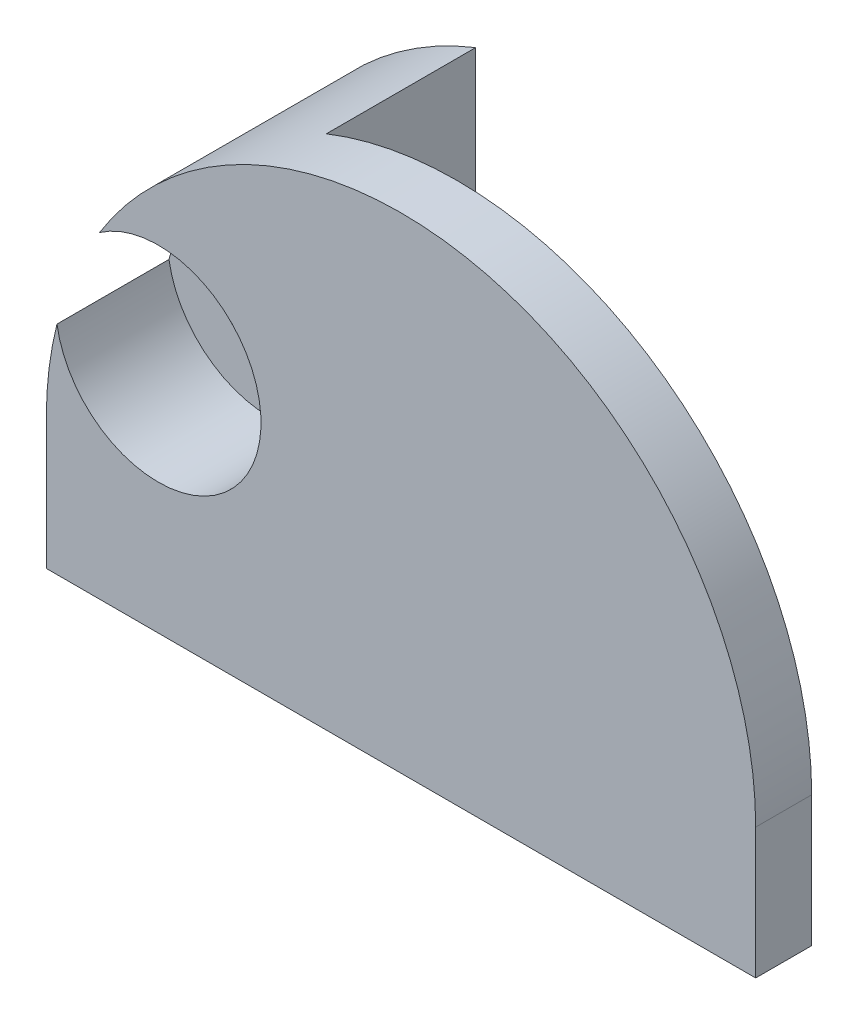
SolidWorks part; units mm, degrees
ref_plane "Plano frontal" through (0, 0, 0) normal (0, 0, 1) x (1, 0, 0)
ref_plane "Plano superior" through (0, 0, 0) normal (0, 1, 0) x (1, 0, 0)
ref_plane "Plano direito" through (0, 0, 0) normal (1, 0, 0) x (0, 0, -1)
sketch "Esboço1" plane through (0, 0, 0) normal (0, 0, 1) x (1, 0, 0)
  line L0 (-9.5, 0) -> (-9.5, -3.5)
  line L1 (-9.5, -3.5) -> (9.5, -3.5)
  line L2 (9.5, -3.5) -> (9.5, 0)
  arc A0 (-9.5, 0) -> (9.5, 0) centre (0, 0) cw
  circle A1 centre (-6.5, 2.75) radius 1.5
  point P8 (8.5688, 2.75)
  point P9 (0, 0)
  dimension "D1" = 9.5
  dimension "D4" = 3
  dimension "D2" = 2.75
  dimension "D3" = 6.5
  dimension "D5" = 3.5
extrude "Ressalto-extrusão1" add sketch "Esboço1" along normal blind 5.5
sketch "Esboço2" plane through (0, 0, 0) normal (0, 0, -1) x (-1, 0, 0)
  line L0 (9.5, 0) -> (9.5, -3.5) construction
  line L1 (-9.5, 11.0468) -> (3.5, 11.0468)
  line L2 (-9.5, 11.0468) -> (-9.5, -3.5)
  line L3 (-9.5, -3.5) -> (3.5, -3.5)
  line L4 (3.5, 11.0468) -> (3.5, -3.5)
  line L5 (-9.5, 11.0468) -> (3.5, -3.5) construction
  line L6 (-9.5, -3.5) -> (3.5, 11.0468) construction
  point P0 (-3, 3.7734)
  point P7 (-9.5, -3.2012)
  point P8 (-9.5, -3.5)
  dimension "D1" = 6
extrude "Corte-extrusão1" cut sketch "Esboço2" against normal blind 4
sketch "Esboço3" plane through (0, 0, 5.5) normal (0, 0, 1) x (1, 0, 0)
  circle A0 centre (-6.5, 2.75) radius 2.75
  dimension "D1" = 5.5
extrude "Corte-extrusão2" cut sketch "Esboço3" against normal blind 3
